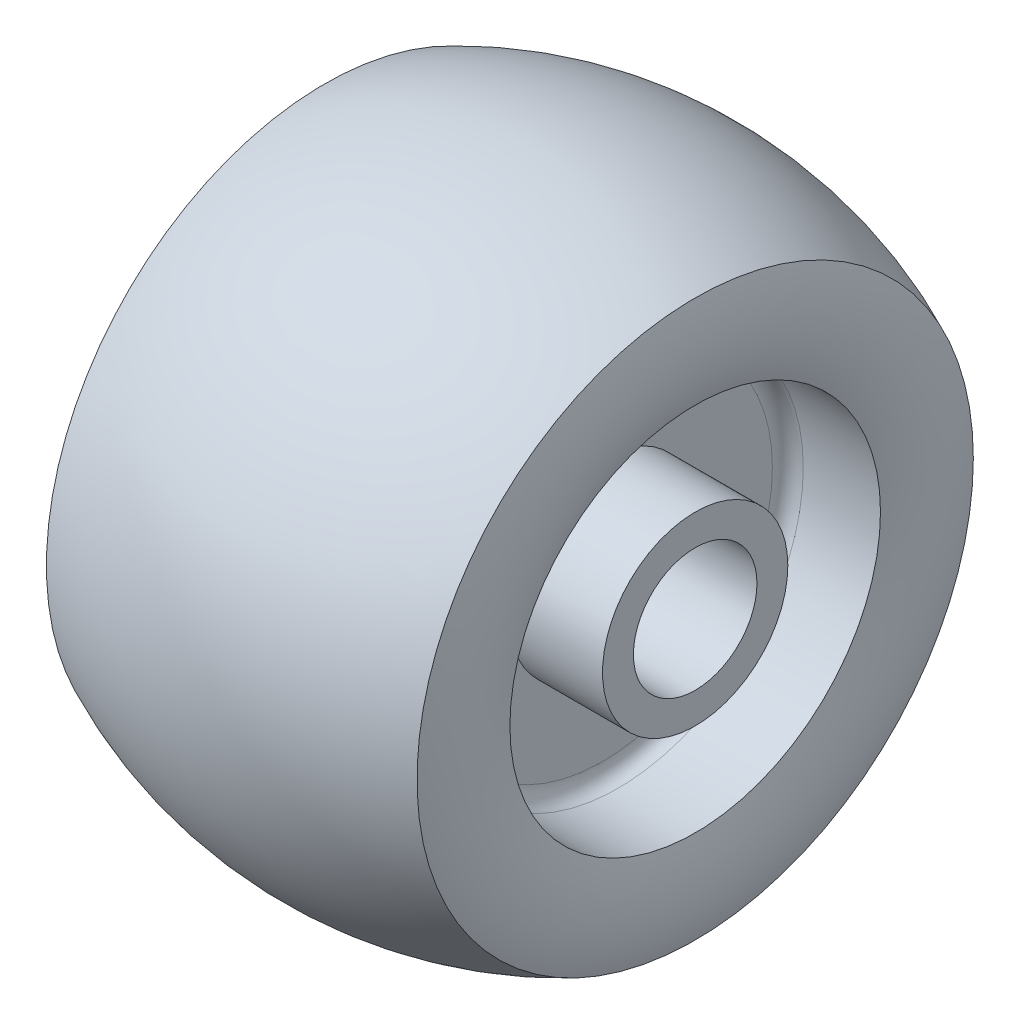
SolidWorks part; units mm, degrees
ref_plane "Front Plane" through (0, 0, 0) normal (0, 0, 1) x (1, 0, 0)
ref_plane "Top Plane" through (0, 0, 0) normal (0, 1, 0) x (1, 0, 0)
ref_plane "Right Plane" through (0, 0, 0) normal (1, 0, 0) x (0, 0, -1)
sketch "Sketch1" plane through (0, 0, 0) normal (0, 0, 1) x (1, 0, 0)
  line L0 (0, 0) -> (-50, 0)
  line L1 (0, 0) -> (50, 0)
  line L2 (-50, 0) -> (-50, 10)
  line L3 (-50, 10) -> (-30, 10)
  line L4 (-30, 10) -> (-30, 55)
  line L5 (-35, 60) -> (-60, 60)
  line L6 (0, -49.5347) -> (0, 49.5347) construction
  line L7 (35, 60) -> (60, 60)
  line L8 (30, 10) -> (30, 55)
  line L9 (50, 10) -> (30, 10)
  line L10 (50, 0) -> (50, 10)
  line L11 (0, 0) -> (0, 103.3616) construction
  arc A0 (-30, 55) -> (-35, 60) centre (-35, 55) ccw
  arc A1 (-60, 60) -> (-60, 90.0631) centre (-14.8547, 75.0315) cw
  arc A2 (60, 60) -> (60, 90.0631) centre (14.8547, 75.0315) ccw
  arc A3 (30, 55) -> (35, 60) centre (35, 55) cw
  arc A4 (-60, 90.0631) -> (60, 90.0631) centre (0, -38.641) cw
  point P10 (-30, 60)
  dimension "D7" = 5
  dimension "D1" = 50
  dimension "D3" = 10
  dimension "D4" = 20
  dimension "D5" = 50
  dimension "D6" = 30
revolve "Revolve1" add sketch "Sketch1" angle 360 about L0
sketch "Sketch2" plane through (50, 0, 0) normal (1, 0, 0) x (0, 0, -1)
  circle A0 centre (0, 0) radius 30
extrude "Boss-Extrude1" add sketch "Sketch2" against normal through all
sketch "Sketch3" plane through (50, 0, 0) normal (1, 0, 0) x (0, 0, -1)
  circle A0 centre (0, 0) radius 30
extrude "Boss-Extrude2" add sketch "Sketch3" along normal blind 10
sketch "Sketch4" plane through (-62.4367, 0, 0) normal (-1, 0, 0) x (0, 0, 1)
  circle A0 centre (0, 0) radius 20
extrude "Cut-Extrude1" cut sketch "Sketch4" against normal through all
